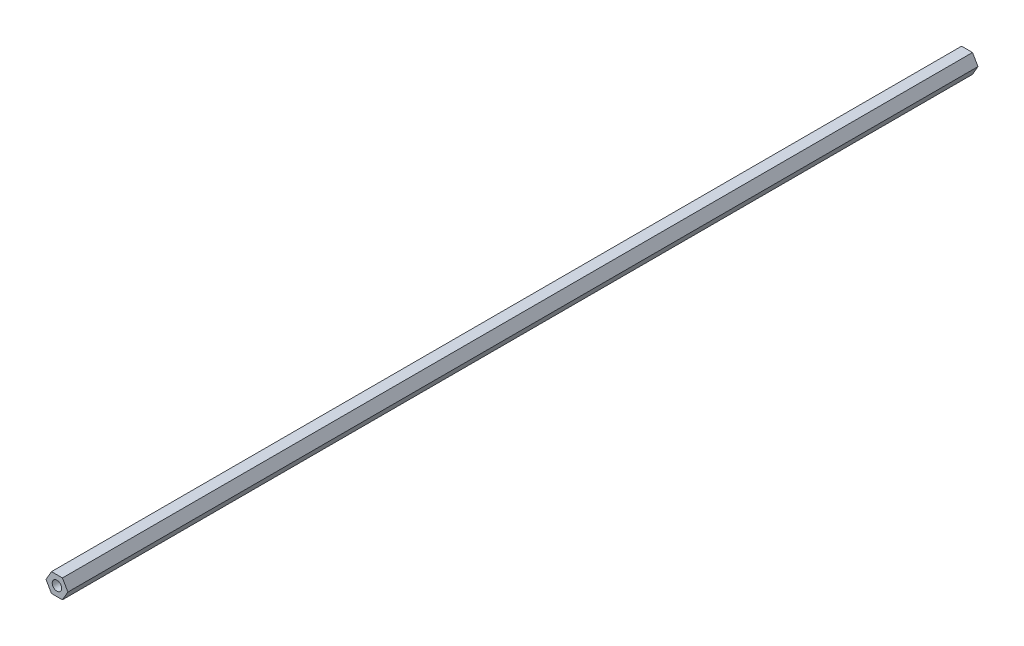
SolidWorks part; units mm, degrees
material "1060 Alloy"
ref_plane "Front Plane" through (0, 0, 0) normal (0, 0, 1) x (1, 0, 0)
ref_plane "Top Plane" through (0, 0, 0) normal (0, 1, 0) x (1, 0, 0)
ref_plane "Right Plane" through (0, 0, 0) normal (1, 0, 0) x (0, 0, -1)
sketch "Sketch1" plane through (0, 0, 0) normal (0, 0, 1) x (1, 0, 0)
  line L1 (-3.6662, 6.35) -> (-7.3323, 0)
  line L2 (-7.3323, 0) -> (-3.6662, -6.35)
  line L3 (-3.6662, -6.35) -> (3.6662, -6.35)
  line L4 (3.6662, -6.35) -> (7.3323, 0)
  line L5 (7.3323, 0) -> (3.6662, 6.35)
  line L6 (3.6662, 6.35) -> (-3.6662, 6.35)
  circle A0 centre (0, 0) radius 6.35 construction
  circle A1 centre (0, 0) radius 3.175
  dimension "D2" = 6.35
  dimension "D1" = 12.7
extrude "Boss-Extrude1" add sketch "Sketch1" along normal blind 609.6
